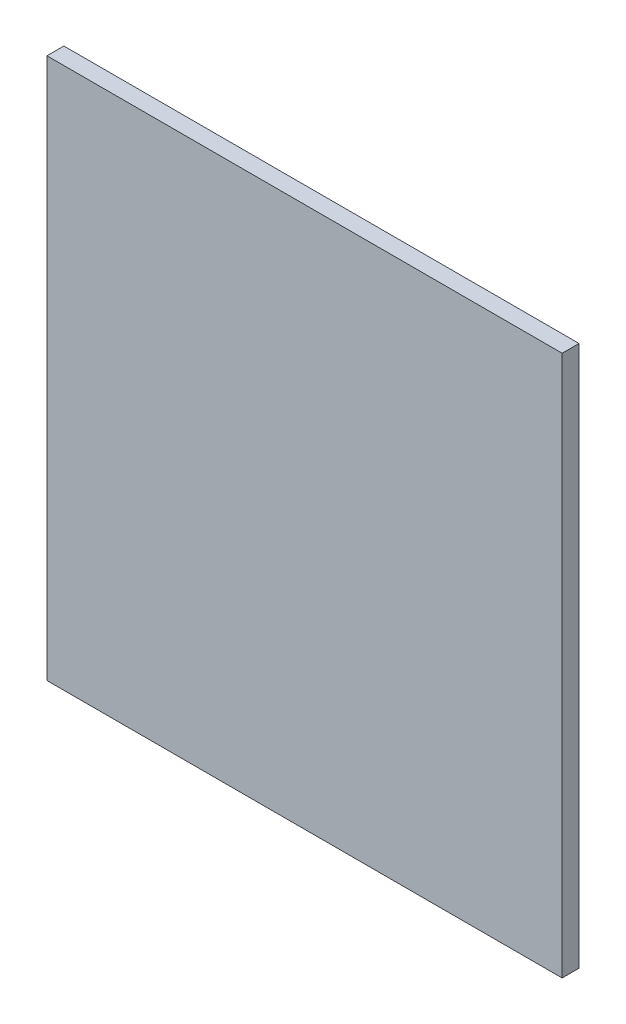
SolidWorks part; units mm, degrees
material "AISI 316 Annealed Stainless Steel Bar (SS)"
ref_plane "Front Plane" through (0, 0, 0) normal (0, 0, 1) x (1, 0, 0)
ref_plane "Top Plane" through (0, 0, 0) normal (0, 1, 0) x (1, 0, 0)
ref_plane "Right Plane" through (0, 0, 0) normal (1, 0, 0) x (0, 0, -1)
sketch "Sketch1" plane through (0, 0, 0) normal (0, 0, 1) x (1, 0, 0)
  line L1 (0, 0) -> (193.49, 0)
  line L2 (0, 0) -> (0, 203.2)
  line L3 (0, 203.2) -> (193.49, 203.2)
  line L4 (193.49, 0) -> (193.49, 203.2)
  dimension "D1" = 193.49
  dimension "D2" = 203.2
extrude "Boss-Extrude1" add sketch "Sketch1" along normal blind 6.35
